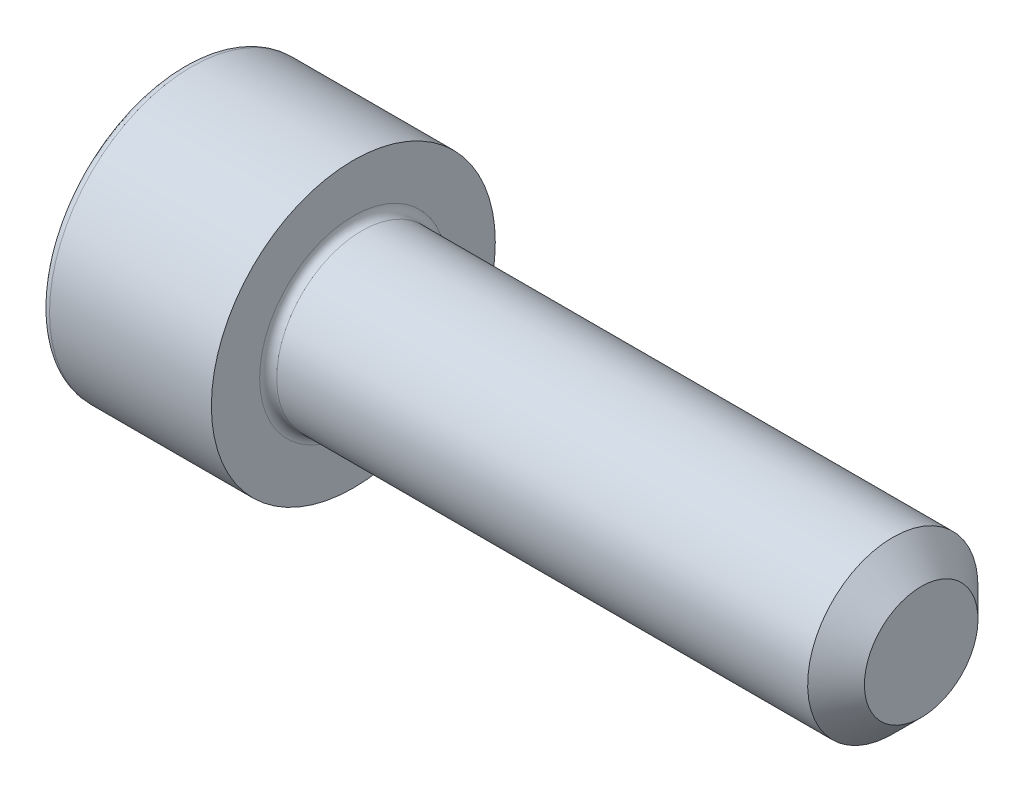
SolidWorks part; units mm, degrees
ref_plane "Спереди" through (0, 0, 0) normal (0, 0, 1) x (1, 0, 0)
ref_plane "Сверху" through (0, 0, 0) normal (0, 1, 0) x (1, 0, 0)
ref_plane "Справа" through (0, 0, 0) normal (1, 0, 0) x (0, 0, -1)
sketch "Эскиз1" plane through (0, 0, 0) normal (0, 0, 1) x (1, 0, 0)
  line L0 (0, 0) -> (0, 5)
  line L1 (0, 5) -> (6, 5)
  line L2 (6, 5) -> (6, 3)
  line L3 (6, 3) -> (26, 3)
  line L4 (26, 3) -> (26, 0)
  line L5 (26, 0) -> (0, 0) construction
  line L6 (0, 0) -> (26, 0)
  dimension "D1" = 10
  dimension "D2" = 6
  dimension "D3" = 6
  dimension "D4" = 20
revolve "Повернуть1" add sketch "Эскиз1" angle 360 about L5
cosmetic thread "Условное изображение резьбы1" parameters "D2"=4.891
sketch "Эскиз2" plane through (0, 0, 0) normal (-1, 0, 0) x (0, 0, 1)
  line L1 (-1.4434, 2.5) -> (-2.8868, 0)
  line L2 (-2.8868, 0) -> (-1.4434, -2.5)
  line L3 (-1.4434, -2.5) -> (1.4434, -2.5)
  line L4 (1.4434, -2.5) -> (2.8868, 0)
  line L5 (2.8868, 0) -> (1.4434, 2.5)
  line L6 (1.4434, 2.5) -> (-1.4434, 2.5)
  circle A0 centre (0, 0) radius 2.5 construction
  dimension "D1" = 5
extrude "Вырез-Вытянуть1" cut sketch "Эскиз2" against normal blind 2.5
fillet "Скругление1" radius 0.3 2 edges at (0, 5, 0) (6, 3, 0)
chamfer "Фаска1" distance 1 angle 45 1 edges at (26, 3, 0)
